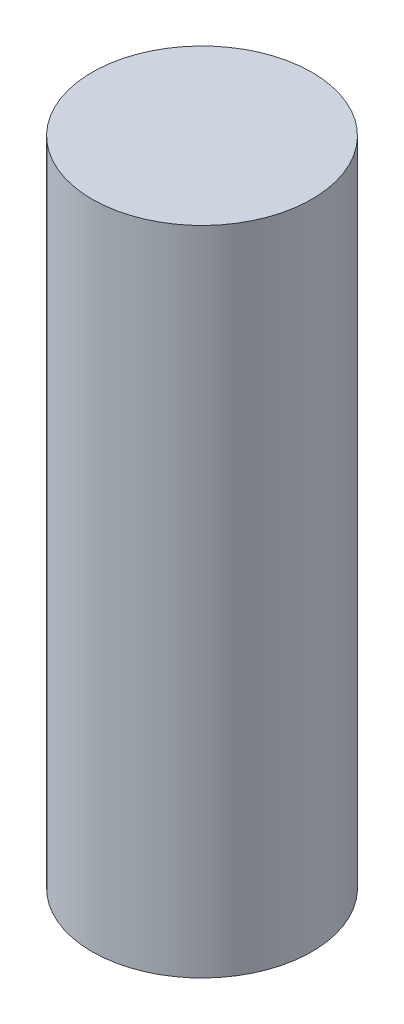
SolidWorks part; units mm, degrees
ref_plane "Front Plane" through (0, 0, 0) normal (0, 0, 1) x (1, 0, 0)
ref_plane "Top Plane" through (0, 0, 0) normal (0, 1, 0) x (1, 0, 0)
ref_plane "Right Plane" through (0, 0, 0) normal (1, 0, 0) x (0, 0, -1)
sketch "Sketch1" plane through (0, 0, 0) normal (0, 1, 0) x (1, 0, 0)
  circle A0 centre (0, 0) radius 7
  dimension "D1" = 14
extrude "Boss-Extrude1" add sketch "Sketch1" along normal mid plane 41.5
